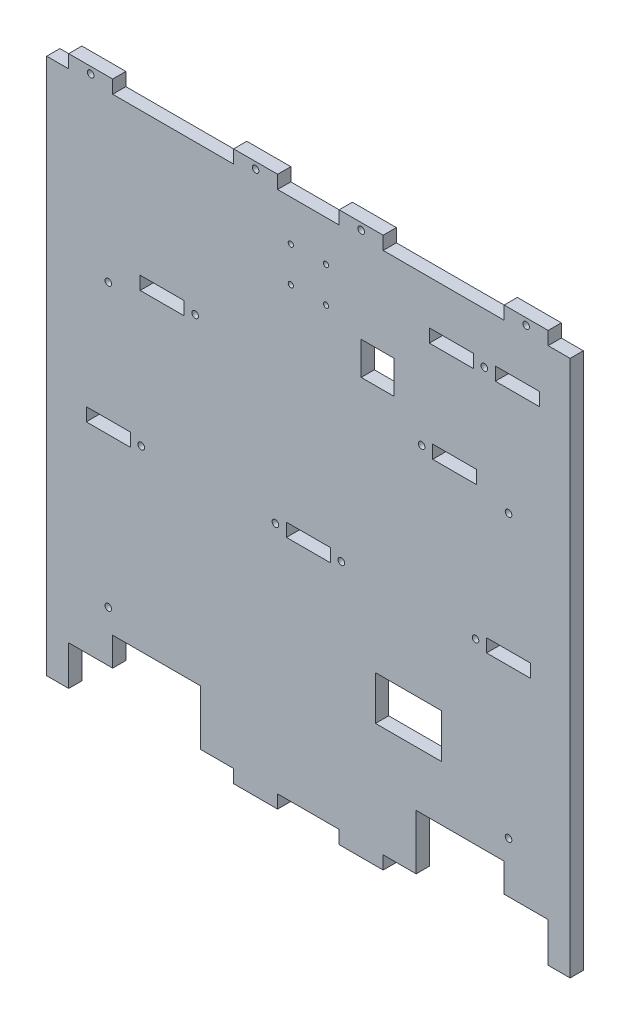
SolidWorks part; units mm, degrees
ref_plane "Plan de face" through (0, 0, 0) normal (0, 0, 1) x (1, 0, 0)
ref_plane "Plan de dessus" through (0, 0, 0) normal (0, 1, 0) x (1, 0, 0)
ref_plane "Plan de droite" through (0, 0, 0) normal (1, 0, 0) x (0, 0, -1)
sketch "Esquisse1" plane through (0, 0, 0) normal (0, 0, 1) x (1, 0, 0)
  line L0 (0, 139.6766) -> (0, -178.3461) construction
  line L1 (-109, 119) -> (109, 119)
  line L2 (-109, 119) -> (-109, -119)
  line L3 (-109, -119) -> (109, -119)
  line L4 (109, 119) -> (109, -119)
  line L5 (-101, -16) -> (-81, -16)
  line L6 (-101, -16) -> (-101, -10)
  line L7 (-101, -10) -> (-81, -10)
  line L8 (-81, -16) -> (-81, -10)
  line L9 (-10, -16) -> (10, -16)
  line L10 (-10, -16) -> (-10, -10)
  line L11 (-10, -10) -> (10, -10)
  line L12 (10, -16) -> (10, -10)
  line L13 (81, -16) -> (101, -16)
  line L14 (81, -16) -> (81, -10)
  line L15 (81, -10) -> (101, -10)
  line L16 (101, -16) -> (101, -10)
  line L17 (-76.5, 54) -> (-56.5, 54)
  line L18 (-76.5, 54) -> (-76.5, 48)
  line L19 (-76.5, 48) -> (-56.5, 48)
  line L20 (-56.5, 54) -> (-56.5, 48)
  line L21 (56.5, 54) -> (76.5, 54)
  line L22 (56.5, 54) -> (56.5, 48)
  line L23 (56.5, 48) -> (76.5, 48)
  line L24 (76.5, 54) -> (76.5, 48)
  line L25 (30.5, -69) -> (60.5, -69)
  line L26 (30.5, -69) -> (30.5, -49)
  line L27 (30.5, -49) -> (60.5, -49)
  line L28 (60.5, -69) -> (60.5, -49)
  line L30 (55, 99) -> (75, 99)
  line L31 (55, 99) -> (55, 93)
  line L32 (55, 93) -> (75, 93)
  line L33 (75, 99) -> (75, 93)
  line L34 (85, 99) -> (105, 99)
  line L35 (85, 99) -> (85, 93)
  line L36 (85, 93) -> (105, 93)
  line L37 (105, 99) -> (105, 93)
  line L38 (24, 64) -> (39, 64)
  line L39 (24, 64) -> (24, 79)
  line L40 (24, 79) -> (39, 79)
  line L41 (39, 64) -> (39, 79)
  dimension "D1" = 238
  dimension "D2" = 218
  dimension "D3" = 109
  dimension "D4" = 119
  dimension "D5" = 20
  dimension "D6" = 6
  dimension "D7" = 6
  dimension "D8" = 20
  dimension "D9" = 20
  dimension "D10" = 6
  dimension "D11" = 103
  dimension "D12" = 8
  dimension "D13" = 8
  dimension "D14" = 99
  dimension "D15" = 103
  dimension "D16" = 103
  dimension "D17" = 20
  dimension "D18" = 6
  dimension "D19" = 6
  dimension "D20" = 20
  dimension "D21" = 167
  dimension "D22" = 167
  dimension "D23" = 32.5
  dimension "D24" = 32.5
  dimension "D25" = 20
  dimension "D26" = 30
  dimension "D27" = 50
  dimension "D28" = 20.5
  dimension "D29" = 6
  dimension "D30" = 6
  dimension "D31" = 20
  dimension "D32" = 20
  dimension "D33" = 20
  dimension "D34" = 20
  dimension "D35" = 10
  dimension "D36" = 4
  dimension "D37" = 15
  dimension "D38" = 15
  dimension "D39" = 70
  dimension "D40" = 40
extrude "Boss.-Extru.1" add sketch "Esquisse1" along normal blind 6
sketch "Esquisse2" plane through (0, 0, 6) normal (0, 0, 1) x (1, 0, 0)
  line L0 (-109, -119) -> (109, -119) construction
  line L1 (-89, -119) -> (-49, -119)
  line L2 (-89, -119) -> (-89, -94)
  line L3 (-89, -94) -> (-49, -94)
  line L4 (-49, -119) -> (-49, -94)
  line L5 (-109, 119) -> (-109, -119) construction
  line L6 (49, -119) -> (89, -119)
  line L7 (49, -119) -> (49, -94)
  line L8 (49, -94) -> (89, -94)
  line L9 (89, -119) -> (89, -94)
  line L10 (109, -119) -> (109, 119) construction
  dimension "D1" = 40
  dimension "D2" = 20
  dimension "D3" = 40
  dimension "D4" = 20
  dimension "D5" = 25
  dimension "D6" = 25
extrude "Enlèv. mat.-Extru.1" cut sketch "Esquisse2" against normal blind 6
sketch "Esquisse3" plane through (0, 0, 6) normal (0, 0, 1) x (1, 0, 0)
  line L0 (0, 157.5653) -> (0, -190.6765) construction
  line L5 (-49, -119) -> (49, -119) construction
  line L6 (-34, -119) -> (-14, -119)
  line L7 (-34, -119) -> (-34, -125)
  line L8 (-34, -125) -> (-14, -125)
  line L9 (-14, -119) -> (-14, -125)
  line L10 (-49, -119) -> (-49, -94) construction
  line L15 (14, -119) -> (14, -125)
  line L16 (34, -125) -> (14, -125)
  line L17 (34, -119) -> (34, -125)
  line L18 (34, -119) -> (14, -119)
  line L19 (198.2674, 0) -> (-212.4835, 0) construction
  line L20 (0, -157.5653) -> (0, 190.6765) construction
  line L21 (34, 125) -> (14, 125)
  line L22 (14, 119) -> (14, 125)
  line L23 (89, 125) -> (109, 125)
  line L24 (89, 125) -> (89, 119)
  line L25 (89, 119) -> (109, 119)
  line L26 (109, 125) -> (109, 119)
  line L27 (-14, 119) -> (-14, 125)
  line L28 (-34, 125) -> (-14, 125)
  line L29 (-34, 119) -> (-34, 125)
  line L30 (-34, 119) -> (-14, 119)
  line L31 (-109, 125) -> (-109, 119)
  line L32 (-89, 119) -> (-109, 119)
  line L33 (-89, 125) -> (-89, 119)
  line L34 (-89, 125) -> (-109, 125)
  line L35 (34, 119) -> (14, 119)
  line L36 (34, 119) -> (34, 125)
  dimension "D2" = 20
  dimension "D3" = 6
  dimension "D4" = 15
extrude "Boss.-Extru.3" add sketch "Esquisse3" against normal blind 6
sketch "Esquisse4" plane through (0, 0, 6) normal (0, 0, 1) x (1, 0, 0)
  line L0 (-111.0944, 51) -> (126.4062, 51) construction
  line L1 (116.6655, -13) -> (-122.9189, -13) construction
  line L3 (0, 153.5677) -> (0, -173.1111) construction
  line L4 (45.0686, 96) -> (109.1297, 96) construction
  line L5 (81, -10) -> (81, -16) construction
  line L6 (10, -16) -> (10, -10) construction
  line L7 (-10, -10) -> (-10, -16) construction
  line L8 (75, 93) -> (75, 99) construction
  line L9 (-114.2336, 122) -> (-6.2018, 122) construction
  line L10 (-56.5, 54) -> (-76.5, 54) construction
  line L11 (-89, 125) -> (-109, 125) construction
  line L12 (-34, 125) -> (-34, 119) construction
  line L13 (55, 93) -> (75, 93) construction
  line L14 (-89, 119) -> (-89, 125) construction
  line L15 (-81, -10) -> (-101, -10) construction
  line L16 (-91, 66.959) -> (-91, -106.1689) construction
  line L17 (-49, -94) -> (-89, -94) construction
  line L18 (-109, 125) -> (-109, -119) construction
  line L19 (56.5, 54) -> (56.5, 48) construction
  circle A0 centre (-15, -13) radius 1.5
  circle A1 centre (-76, -13) radius 1.5
  circle A2 centre (80, 96) radius 1.5
  circle A3 centre (51.5, 51) radius 1.5
  circle A4 centre (76, -13) radius 1.5
  circle A5 centre (15, -13) radius 1.5
  circle A6 centre (-51.5, 51) radius 1.5
  circle A7 centre (-99, 122) radius 1.5
  circle A8 centre (-24, 122) radius 1.5
  circle A9 centre (24, 122) radius 1.5
  circle A10 centre (99, 122) radius 1.5
  circle A11 centre (-91, -84) radius 1.5
  circle A12 centre (-91, 44) radius 1.5
  circle A13 centre (91, -84) radius 1.5
  circle A14 centre (91, 44) radius 1.5
  dimension "D2" = 5
  dimension "D3" = 3
  dimension "D4" = 3
  dimension "D5" = 5
  dimension "D6" = 5
  dimension "D7" = 3
  dimension "D8" = 3
  dimension "D9" = 3
  dimension "D10" = 5
  dimension "D11" = 3
  dimension "D12" = 5
  dimension "D13" = 3
  dimension "D15" = 3
  dimension "D16" = 3
  dimension "D17" = 10
  dimension "D18" = 10
  dimension "D19" = 3
  dimension "D20" = 3
  dimension "D21" = 3
  dimension "D22" = 128
  dimension "D14" = 3
  dimension "D23" = 10
  dimension "D24" = 18
extrude "Enlèv. mat.-Extru.2" cut sketch "Esquisse4" against normal blind 6
sketch "Esquisse5" plane through (0, 0, 6) normal (0, 0, 1) x (1, 0, 0)
  line L0 (-109, 119) -> (-109, -125)
  line L1 (-109, 119) -> (-119, 119)
  line L2 (-109, -125) -> (-119, -125)
  line L3 (-119, 119) -> (-119, -125)
  line L5 (109, -125) -> (109, 119)
  line L6 (109, -125) -> (119, -125)
  line L7 (109, 119) -> (119, 119)
  line L8 (119, -125) -> (119, 119)
  line L11 (109, 125) -> (89, 125) construction
  line L12 (-89, 125) -> (-109, 125) construction
  dimension "D1" = 10
  dimension "D2" = 10
  dimension "D3" = 244
  dimension "D4" = 244
  dimension "D5" = 6
  dimension "D6" = 6
extrude "Boss.-Extru.4" add sketch "Esquisse5" against normal blind 6
sketch "Esquisse6" plane through (0, 0, 6) normal (0, 0, 1) x (1, 0, 0)
  line L0 (0, 108.4917) -> (0, -172.5759) construction
  line L1 (89, -119) -> (109, -119)
  line L2 (89, -119) -> (89, -107)
  line L3 (89, -107) -> (109, -107)
  line L4 (109, -119) -> (109, -107)
  line L5 (-109, -119) -> (-109, -107)
  line L6 (-89, -107) -> (-109, -107)
  line L7 (-89, -119) -> (-89, -107)
  line L8 (-89, -119) -> (-109, -119)
  dimension "D1" = 12
  dimension "D2" = 20
extrude "Enlèv. mat.-Extru.3" cut sketch "Esquisse6" against normal blind 6
sketch "Esquisse7" plane through (0, 0, 6) normal (0, 0, 1) x (1, 0, 0)
  line L0 (14, 119) -> (-14, 119) construction
  line L1 (14, 125) -> (14, 119) construction
  circle A0 centre (-8, 100.5) radius 1.175
  circle A1 centre (8, 100.5) radius 1.175
  circle A2 centre (-8, 84.5) radius 1.175
  circle A3 centre (8, 84.5) radius 1.175
  dimension "D1" = 16
  dimension "D7" = 2.35
  dimension "D8" = 2.35
  dimension "D9" = 2.35
  dimension "D10" = 2.35
  dimension "D2" = 16
  dimension "D3" = 16
  dimension "D4" = 16
  dimension "D5" = 18.5
  dimension "D6" = 6
  dimension "D11" = 18.5
extrude "Enlèv. mat.-Extru.4" cut sketch "Esquisse7" against normal through all
equation "\"D3@Esquisse1\"=\"D2@Esquisse1\"/2"
equation "\"D4@Esquisse1\"=\"D1@Esquisse1\"/2"
